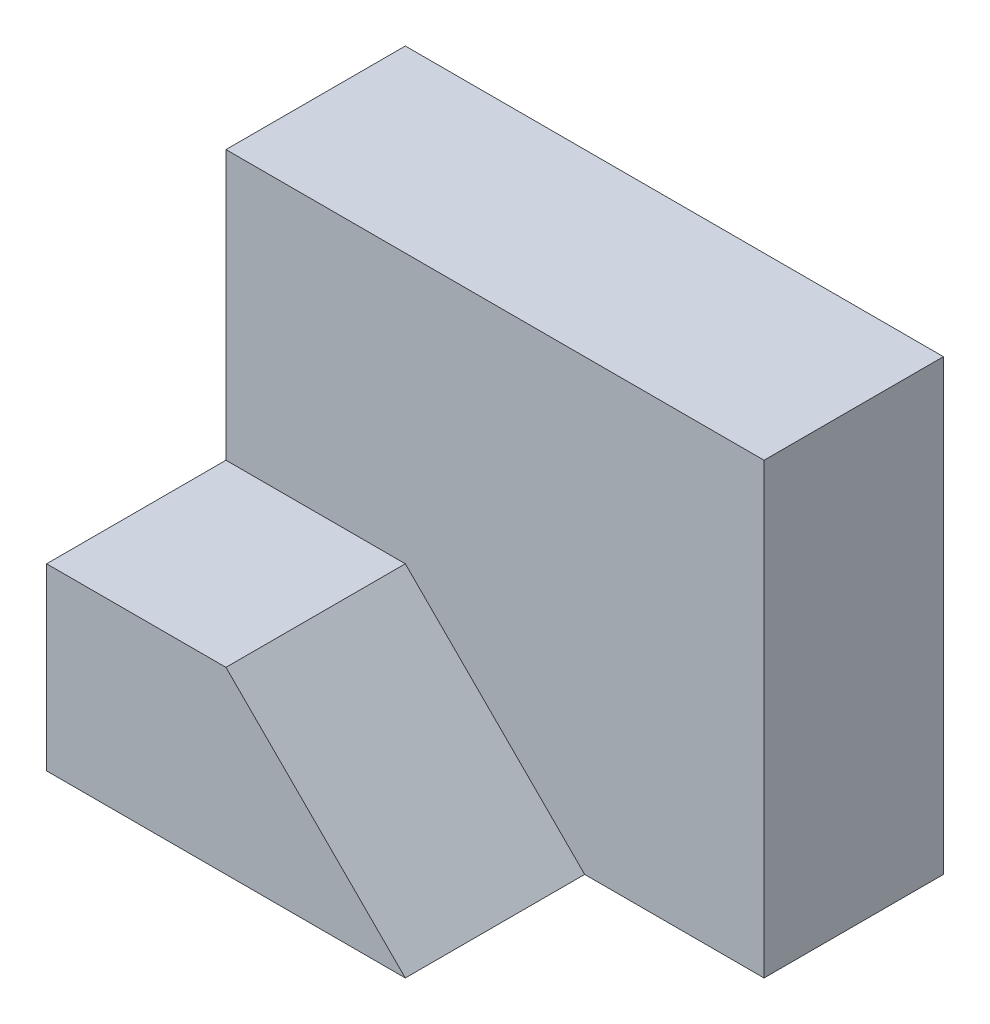
SolidWorks part; units mm, degrees
ref_plane "Front Plane" through (0, 0, 0) normal (0, 0, 1) x (1, 0, 0)
ref_plane "Top Plane" through (0, 0, 0) normal (0, 1, 0) x (1, 0, 0)
ref_plane "Right Plane" through (0, 0, 0) normal (1, 0, 0) x (0, 0, -1)
sketch "Sketch1" plane through (0, 0, 0) normal (0, 0, 1) x (1, 0, 0)
  line L1 (0, 0) -> (6, 0)
  line L2 (0, 0) -> (0, 5)
  line L3 (0, 5) -> (6, 5)
  line L4 (6, 0) -> (6, 5)
  dimension "D1" = 6
  dimension "D2" = 5
extrude "Boss-Extrude1" add sketch "Sketch1" along normal blind 2
sketch "Sketch2" plane through (0, 0, 2) normal (0, 0, 1) x (1, 0, 0)
  line L0 (0, 0) -> (0, 2)
  line L1 (0, 5) -> (0, 0) construction
  line L2 (0, 2) -> (2, 2)
  line L3 (2, 2) -> (4, 0)
  line L4 (0, 0) -> (6, 0) construction
  line L5 (4, 0) -> (0, 0)
  dimension "D1" = 2
  dimension "D2" = 4
  dimension "D3" = 2
extrude "Boss-Extrude2" add sketch "Sketch2" along normal blind 2
